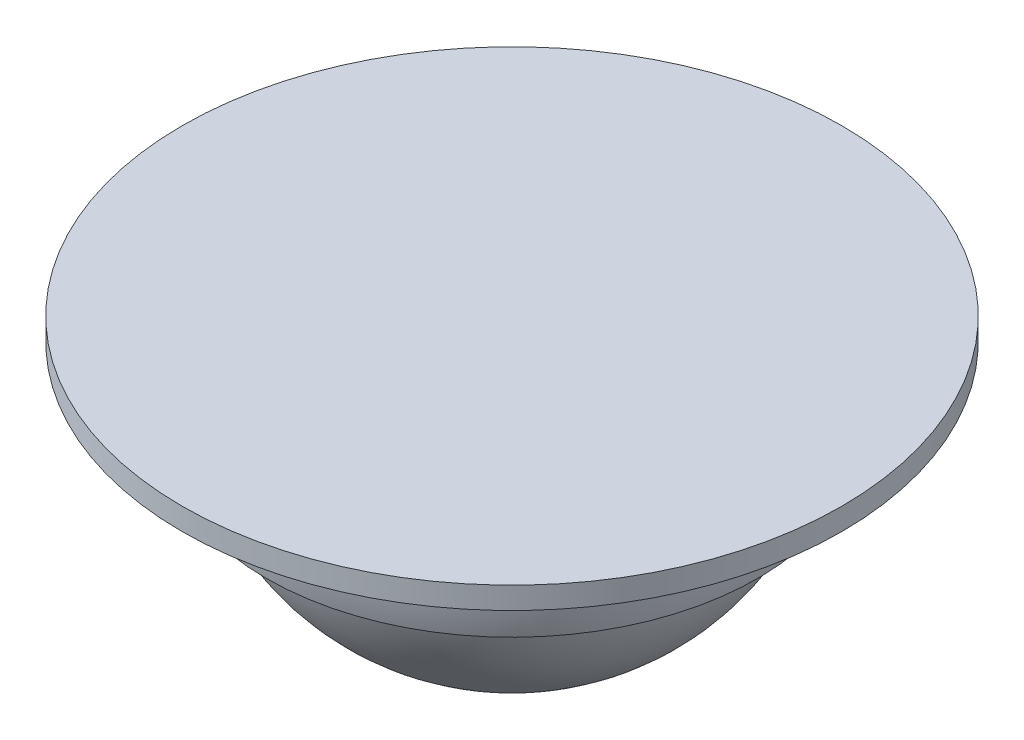
SolidWorks part; units mm, degrees
ref_plane "Front Plane" through (0, 0, 0) normal (0, 0, 1) x (1, 0, 0)
ref_plane "Top Plane" through (0, 0, 0) normal (0, 1, 0) x (1, 0, 0)
ref_plane "Right Plane" through (0, 0, 0) normal (1, 0, 0) x (0, 0, -1)
sketch "Sketch1" plane through (0, 0, 0) normal (0, 0, 1) x (1, 0, 0)
  line L0 (0, 0) -> (0, -22.0504) construction
  line L1 (0, 0) -> (-30, 0)
  line L2 (-30, 0) -> (-30, -2)
  line L3 (-30, -2) -> (-22.9129, -2)
  line L4 (0, 0) -> (0, -25)
  line L5 (-20.2572, -9.5359) -> (-22.3238, -9.5359)
  arc A0 (-22.9129, -2) -> (-22.3238, -9.5359) centre (0, -4) ccw
  arc A1 (0, -25) -> (-20.2572, -9.5359) centre (0, -4) cw
  dimension "D3" = 21
  dimension "D4" = 23
  dimension "D1" = 25
  dimension "D2" = 2
  dimension "D5" = 30
revolve "Revolve1" add sketch "Sketch1" angle 360 about L0
